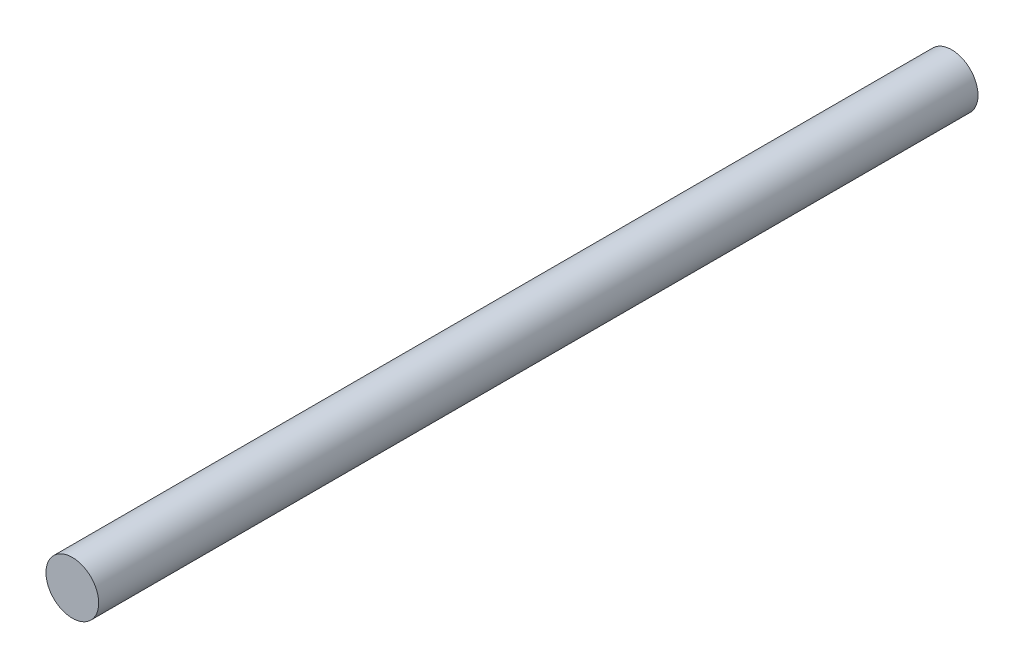
SolidWorks part; units mm, degrees
ref_plane "Спереди" through (0, 0, 0) normal (0, 0, 1) x (1, 0, 0)
ref_plane "Сверху" through (0, 0, 0) normal (0, 1, 0) x (1, 0, 0)
ref_plane "Справа" through (0, 0, 0) normal (1, 0, 0) x (0, 0, -1)
sketch "Эскиз1" plane through (0, 0, 0) normal (0, 0, 1) x (1, 0, 0)
  circle A0 centre (0, 0) radius 3
extrude "Бобышка-Вытянуть1" add sketch "Эскиз1" along normal blind 100
